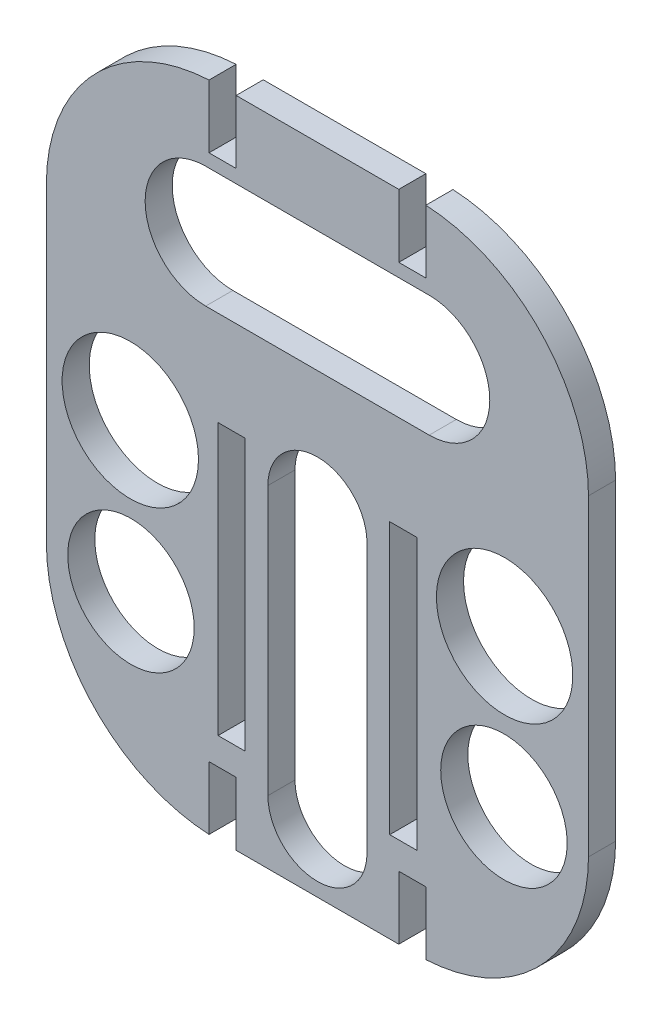
SolidWorks part; units mm, degrees
ref_plane "Front Plane" through (0, 0, 0) normal (0, 0, 1) x (1, 0, 0)
ref_plane "Top Plane" through (0, 0, 0) normal (0, 1, 0) x (1, 0, 0)
ref_plane "Right Plane" through (0, 0, 0) normal (1, 0, 0) x (0, 0, -1)
sketch "Sketch1" plane through (0, 0, 0) normal (0, 0, 1) x (1, 0, 0)
  line L0 (-11.5217, -45.7473) -> (11.5217, -45.7473)
  line L1 (-11.5217, -45.7473) -> (-11.5217, 26.6073) construction
  line L2 (-11.5217, 26.6073) -> (11.5217, 26.6073)
  line L3 (11.5217, -45.7473) -> (11.5217, 26.6073) construction
  line L4 (-11.5217, -45.7473) -> (11.5217, 26.6073) construction
  line L5 (-11.5217, 26.6073) -> (11.5217, -45.7473) construction
  line L6 (-30, -26.8746) -> (30, -26.8746) construction
  line L7 (-30, -26.8746) -> (-30, 7.7346)
  line L8 (-30, 7.7346) -> (30, 7.7346) construction
  line L9 (30, -26.8746) -> (30, 7.7346)
  line L10 (-30, -26.8746) -> (30, 7.7346) construction
  line L11 (-30, 7.7346) -> (30, -26.8746) construction
  arc A0 (-30, 7.7346) -> (-11.5217, 26.6073) centre (-11.0004, 7.6144) cw
  arc A1 (11.5217, 26.6073) -> (30, 7.7346) centre (11.0004, 7.6144) cw
  arc A2 (-30, -26.8746) -> (-11.5217, -45.7473) centre (-11.0004, -26.7544) ccw
  arc A3 (11.5217, -45.7473) -> (30, -26.8746) centre (11.0004, -26.7544) ccw
  point P0 (0, -9.57)
  point P6 (0, -9.57)
  dimension "D5" = 19
  dimension "D6" = 19
  dimension "D7" = 19
  dimension "D8" = 19
  dimension "D1" = 72.3545
  dimension "D2" = 60
  dimension "D3" = 23.0434
  dimension "D4" = 34.6091
  dimension "D9" = 9.57
extrude "Boss-Extrude1" add sketch "Sketch1" along normal blind 3 contours A1 L9 A3 L0 A2 L7 A0 L2
sketch "Sketch2" plane through (0, 0, 3) normal (0, 0, 1) x (1, 0, 0)
  line L0 (-11.5217, -45.7473) -> (11.5217, -45.7473) construction
  line L1 (-11, -35.7473) -> (-8, -35.7473)
  line L2 (-11, -35.7473) -> (-11, -5.7473)
  line L3 (-11, -5.7473) -> (-8, -5.7473)
  line L4 (-8, -35.7473) -> (-8, -5.7473)
  line L5 (0, -1.65) -> (0, 1.65) construction
  line L6 (11, -5.7473) -> (8, -5.7473)
  line L7 (8, -35.7473) -> (8, -5.7473)
  line L8 (11, -35.7473) -> (8, -35.7473)
  line L9 (11, -35.7473) -> (11, -5.7473)
  line L10 (-12.3673, 11.4364) -> (12.3673, 11.4364) construction
  line L11 (-12.3673, 18.1398) -> (12.3673, 18.1398)
  line L12 (-12.3673, 4.733) -> (12.3673, 4.733)
  line L13 (0, -9.0271) -> (0, -38.7473) construction
  line L14 (5.4846, -9.0271) -> (5.4846, -38.7473)
  line L15 (-5.4846, -9.0271) -> (-5.4846, -38.7473)
  line L16 (12, -38.7473) -> (9, -38.7473)
  line L17 (-12, -45.7473) -> (-9, -45.7473)
  line L18 (-12, -45.7473) -> (-12, -38.7473)
  line L19 (-12, -38.7473) -> (-9, -38.7473)
  line L20 (-9, -45.7473) -> (-9, -38.7473)
  line L21 (9, -45.7473) -> (9, -38.7473)
  line L22 (12, -45.7473) -> (9, -45.7473)
  line L23 (12, -45.7473) -> (12, -38.7473)
  line L24 (-11.5217, 26.6073) -> (11.5217, 26.6073) construction
  line L25 (-12, 26.6073) -> (-9, 26.6073)
  line L26 (-12, 26.6073) -> (-12, 19.6073)
  line L27 (-12, 19.6073) -> (-9, 19.6073)
  line L28 (-9, 26.6073) -> (-9, 19.6073)
  line L29 (12, 19.6073) -> (9, 19.6073)
  line L30 (9, 26.6073) -> (9, 19.6073)
  line L31 (12, 26.6073) -> (9, 26.6073)
  line L32 (12, 26.6073) -> (12, 19.6073)
  arc A0 (-12.3673, 18.1398) -> (-12.3673, 4.733) centre (-12.3673, 11.4364) ccw
  arc A1 (12.3673, 4.733) -> (12.3673, 18.1398) centre (12.3673, 11.4364) ccw
  circle A2 centre (-20.7129, -10.3706) radius 7.5463
  circle A3 centre (-20.6412, -26.7548) radius 6.9988
  arc A4 (5.4846, -9.0271) -> (-5.4846, -9.0271) centre (0, -9.0271) ccw
  arc A5 (-5.4846, -38.7473) -> (5.4846, -38.7473) centre (0, -38.7473) ccw
  circle A6 centre (20.6412, -26.7548) radius 6.9988
  circle A7 centre (20.7129, -10.3706) radius 7.5463
  point P14 (0, 11.4364)
  point P25 (0, -23.8872)
  dimension "D5" = 7
  dimension "D1" = 10
  dimension "D2" = 30
  dimension "D3" = 3
  dimension "D4" = 8
  dimension "D6" = 3
  dimension "D7" = 9
  dimension "D8" = 7
  dimension "D9" = 3
  dimension "D10" = 9
extrude "Cut-Extrude1" cut sketch "Sketch2" against normal through all both
